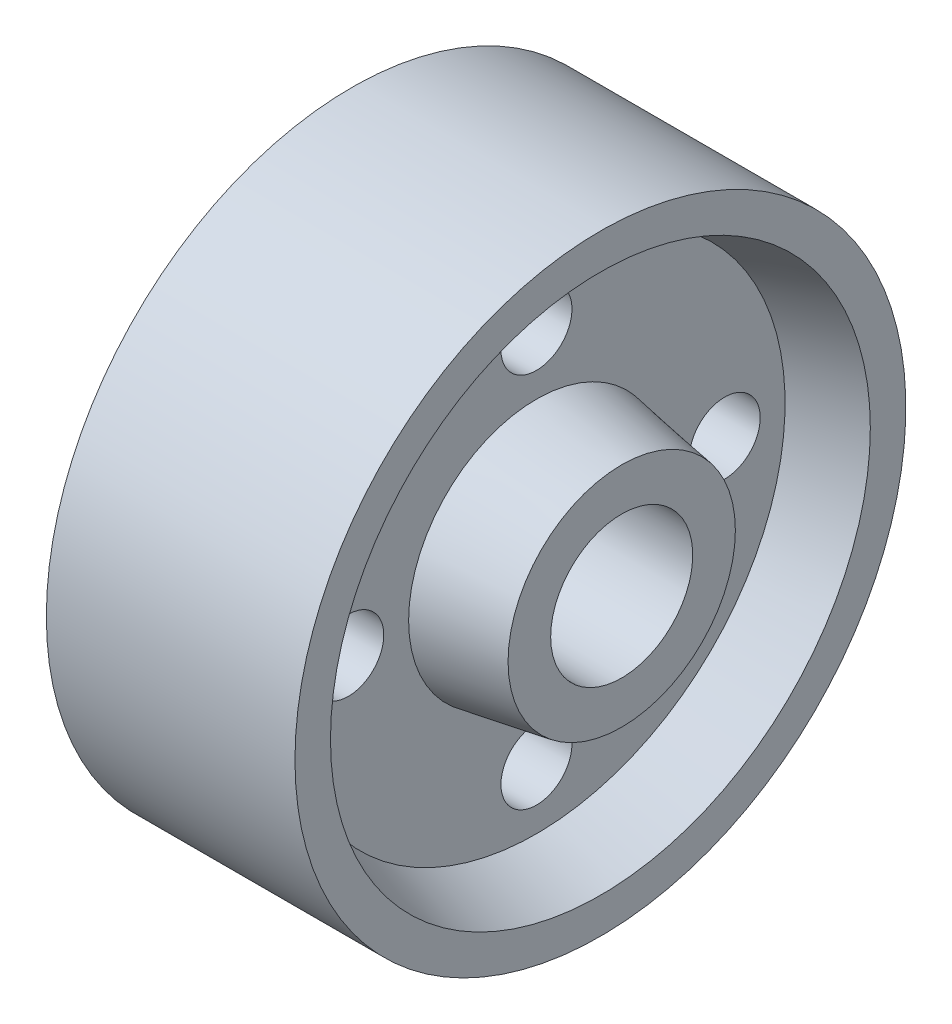
SolidWorks part; units mm, degrees
ref_plane "Front Plane" through (0, 0, 0) normal (0, 0, 1) x (1, 0, 0)
ref_plane "Top Plane" through (0, 0, 0) normal (0, 1, 0) x (1, 0, 0)
ref_plane "Right Plane" through (0, 0, 0) normal (1, 0, 0) x (0, 0, -1)
sketch "Sketch1" plane through (0, 0, 0) normal (0, 1, 0) x (1, 0, 0)
  line L0 (0, 0) -> (138.2525, 0) construction
  line L1 (0, 0) -> (0, 16)
  line L2 (0, 16) -> (12, 18)
  line L3 (12, 18) -> (12, 35)
  line L4 (12, 35) -> (3, 38)
  line L5 (3, 38) -> (3, 43)
  line L6 (3, 43) -> (38, 43)
  line L7 (20.5, 43) -> (20.5, 0) construction
  line L8 (41, 0) -> (41, 16)
  line L9 (41, 16) -> (29, 18)
  line L10 (29, 18) -> (29, 35)
  line L11 (29, 35) -> (38, 38)
  line L12 (38, 38) -> (38, 43)
  line L13 (0, 0) -> (41, 0)
  point P16 (0, 0)
  dimension "D1" = 16
  dimension "D2" = 18
  dimension "D3" = 35
  dimension "D4" = 38
  dimension "43" = 43
  dimension "D6" = 12
  dimension "D7" = 17.5
  dimension "D8" = 20.5
revolve "Revolve2" add sketch "Sketch1" angle 360 about L0
sketch "Sketch3" plane through (0, 0, 0) normal (-1, 0, 0) x (0, 0, 1)
  circle A0 centre (0, 0) radius 26.4991 construction
  circle A1 centre (0, 26.4991) radius 5
  circle A2 centre (26.4991, 0) radius 5
  circle A3 centre (0, -26.4991) radius 5
  circle A4 centre (-26.4991, 0) radius 5
  point P5 (-26.4991, 0)
  point P14 (0, 0)
  dimension "D1" = 52.9982
  dimension "D2" = 10
  dimension "D3" = 4
extrude "Cut-Extrude1" cut sketch "Sketch3" against normal through all
sketch "Sketch4" plane through (0, 0, 0) normal (-1, 0, 0) x (0, 0, 1)
  circle A0 centre (0, 0) radius 10
  dimension "D1" = 20
extrude "Cut-Extrude2" cut sketch "Sketch4" against normal through all
